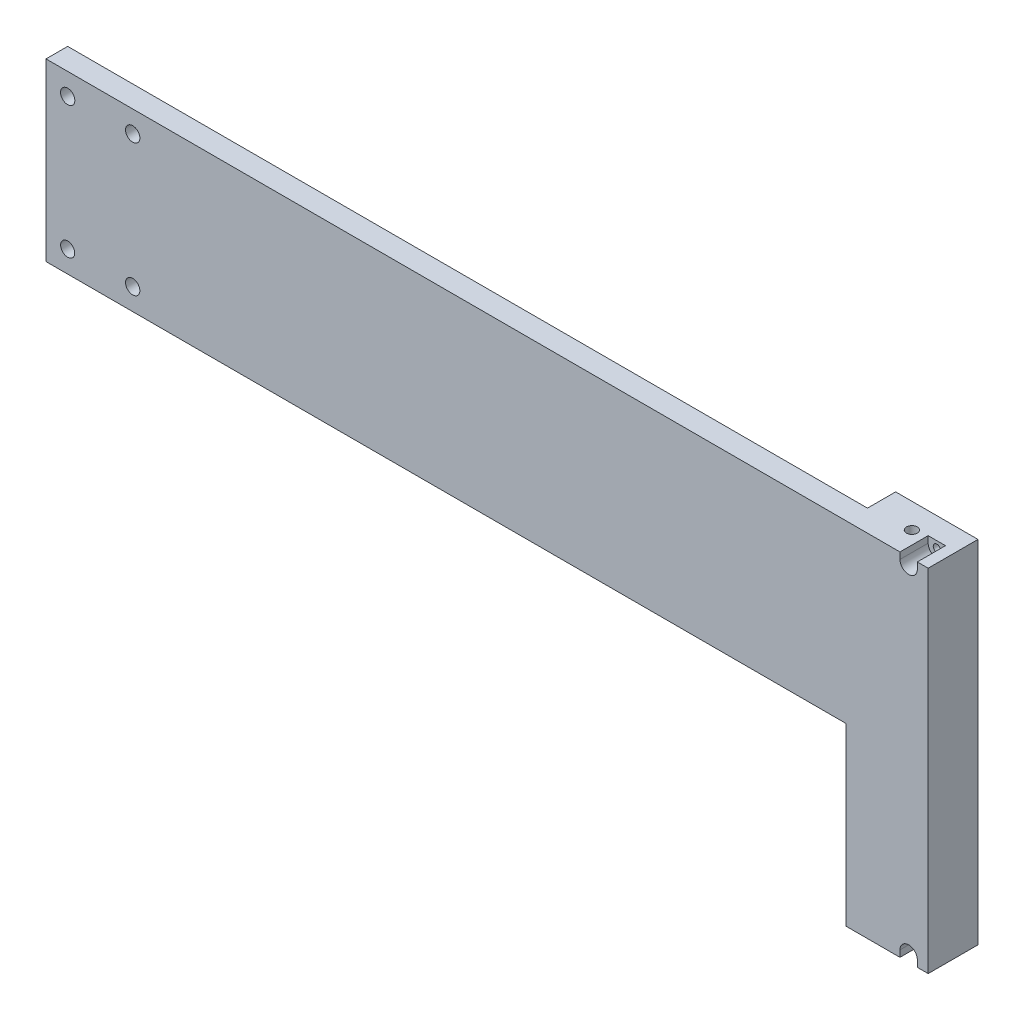
SolidWorks part; units mm, degrees
material "6061 Alloy"
ref_plane "Front Plane" through (0, 0, 0) normal (0, 0, 1) x (1, 0, 0)
ref_plane "Top Plane" through (0, 0, 0) normal (0, 1, 0) x (1, 0, 0)
ref_plane "Right Plane" through (0, 0, 0) normal (1, 0, 0) x (0, 0, -1)
sketch "Sketch1" plane through (0, 0, 0) normal (0, 0, 1) x (1, 0, 0)
  line L1 (0, 0) -> (369, 0)
  line L2 (0, 0) -> (0, 81)
  line L3 (0, 81) -> (369, 81)
  line L4 (369, 0) -> (369, 81)
  dimension "D1" = 81
  dimension "D2" = 369
extrude "Boss-Extrude1" add sketch "Sketch1" along normal blind 10
sketch "Sketch2" plane through (369, 0, 0) normal (1, 0, 0) x (0, 0, -1)
  line L1 (-10, 81) -> (13, 81)
  line L2 (-10, 81) -> (-10, -81)
  line L3 (-10, -81) -> (13, -81)
  line L4 (13, 81) -> (13, -81)
  dimension "D1" = 162
  dimension "D2" = 23
extrude "Boss-Extrude2" add sketch "Sketch2" along normal blind 38
sketch "Sketch3" plane through (0, 81, 0) normal (0, 1, 0) x (1, 0, 0)
  line L0 (407, 13) -> (369, 13) construction
  line L1 (407, 13) -> (407, -10) construction
  circle A0 centre (388, 1.5) radius 2.5
  dimension "D1" = 11.5
  dimension "D2" = 19
  dimension "D3" = 5
extrude "Cut-Extrude1" cut sketch "Sketch3" against normal through all
sketch "Sketch4" plane through (0, 0, 10) normal (0, 0, 1) x (1, 0, 0)
  line L0 (407, 81) -> (407, -81) construction
  line L1 (407, 81) -> (0, 81) construction
  circle A0 centre (398, -78) radius 1.65
  circle A1 centre (398, 78) radius 1.65
  dimension "D1" = 3.3
  dimension "D2" = 9
  dimension "D3" = 3
  dimension "D4" = 3.3
  dimension "D5" = 3
extrude "Cut-Extrude2" cut sketch "Sketch4" against normal through all
sketch "Sketch5" plane through (0, 0, 10) normal (0, 0, 1) x (1, 0, 0)
  line L0 (394, 78) -> (394, 81)
  line L1 (407, 81) -> (0, 81) construction
  line L2 (402, 78) -> (402, 81)
  line L3 (394, 81) -> (402, 81)
  line L4 (394, -78) -> (394, -81)
  line L7 (402, -78) -> (402, -81)
  line L10 (394, -81) -> (402, -81)
  arc A0 (394, 78) -> (402, 78) centre (398, 78) ccw
  arc A1 (402, -78) -> (394, -78) centre (398, -78) ccw
  dimension "D1" = 8
  dimension "D2" = 8
  dimension "D3" = 3
  dimension "D4" = 8
  dimension "D5" = 5
extrude "Cut-Extrude4" cut sketch "Sketch5" against normal blind 13
sketch "Sketch6" plane through (0, 0, 10) normal (0, 0, 1) x (1, 0, 0)
  line L0 (0, 81) -> (0, 0) construction
  line L1 (394, 81) -> (0, 81) construction
  line L2 (0, 0) -> (369, 0) construction
  circle A0 centre (10, 71) radius 3.3
  circle A1 centre (40, 71) radius 3.3
  circle A2 centre (40, 10) radius 3.3
  circle A3 centre (10, 10) radius 3.25
  dimension "D1" = 10
  dimension "D2" = 10
  dimension "D3" = 10
  dimension "D4" = 30
  dimension "D5" = 6.6
  dimension "D6" = 6.6
  dimension "D7" = 6.6
  dimension "D8" = 6.5
extrude "Cut-Extrude5" cut sketch "Sketch6" against normal blind 13
